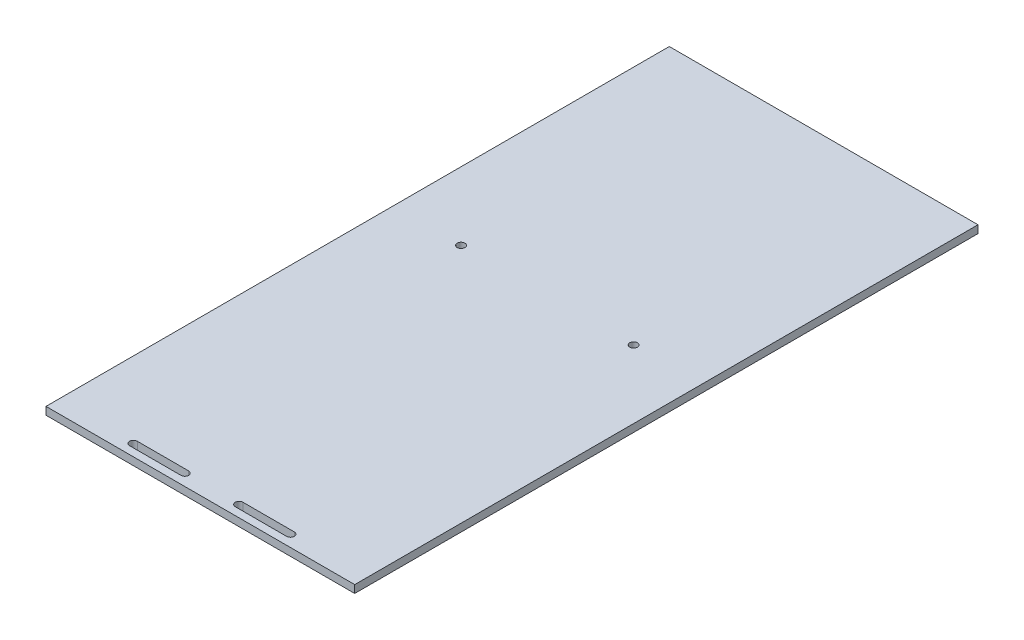
SolidWorks part; units mm, degrees
ref_plane "前视基准面" through (0, 0, 0) normal (0, 0, 1) x (1, 0, 0)
ref_plane "上视基准面" through (0, 0, 0) normal (0, 1, 0) x (1, 0, 0)
ref_plane "右视基准面" through (0, 0, 0) normal (1, 0, 0) x (0, 0, -1)
sketch "草图1" plane through (0, 0, 0) normal (0, 1, 0) x (1, 0, 0)
  line L0 (0, 0) -> (120.1121, 0)
  line L9 (0, 0) -> (0, -242.506)
  line L10 (120.1121, 0) -> (120.1121, -242.506)
  line L11 (0, -242.506) -> (120.1121, -242.506)
  point P2 (122.6487, -248.3178)
  point P5 (120, -3.6616)
  point P6 (121.3165, -243)
  point P8 (0, 0)
  point P10 (0, 0)
  point P11 (0, 0)
  point P12 (0, 0)
  point P13 (0, 0)
  point P14 (0, 0)
  point P15 (1.1411, -243)
extrude "凸台-拉伸1" add sketch "草图1" along normal blind 3 contours L10 L11 L9 L0
sketch "草图3" plane through (0, 3, 0) normal (0, 1, 0) x (1, 0, 0)
  line L0 (29.5, -238) -> (49.5, -238) construction
  line L1 (29.5, -236.5) -> (49.5, -236.5)
  line L2 (29.5, -239.5) -> (49.5, -239.5)
  line L3 (70.6121, -238) -> (90.6121, -238) construction
  line L4 (70.6121, -236.5) -> (90.6121, -236.5)
  line L5 (70.6121, -239.5) -> (90.6121, -239.5)
  line L6 (0, 0) -> (0, -242.506) construction
  line L7 (0, -242.506) -> (120.1121, -242.506) construction
  line L8 (120.1121, 0) -> (120.1121, -242.506) construction
  arc A0 (29.5, -236.5) -> (29.5, -239.5) centre (29.5, -238) ccw
  arc A1 (49.5, -239.5) -> (49.5, -236.5) centre (49.5, -238) ccw
  arc A4 (70.6121, -236.5) -> (70.6121, -239.5) centre (70.6121, -238) ccw
  arc A5 (90.6121, -239.5) -> (90.6121, -236.5) centre (90.6121, -238) ccw
  circle A6 centre (26.5, -107.506) radius 1.5
  circle A7 centre (93.6121, -107.506) radius 1.5
  point P2 (39.5, -238)
  point P9 (80.6121, -238)
  point P20 (0, 0)
  point P21 (0, 0)
  point P26 (27.26, -175.696)
  point P27 (0, 0)
  point P28 (0, 0)
  point P29 (0, 0)
  point P30 (105.1397, -169.7661)
  point P31 (0, 0)
  dimension "D1" = 29.5
  dimension "D2" = 26.5
  dimension "D3" = 135
  dimension "D4" = 26.5
  dimension "D5" = 135
extrude "切除-拉伸5" cut sketch "草图3" against normal blind 3
